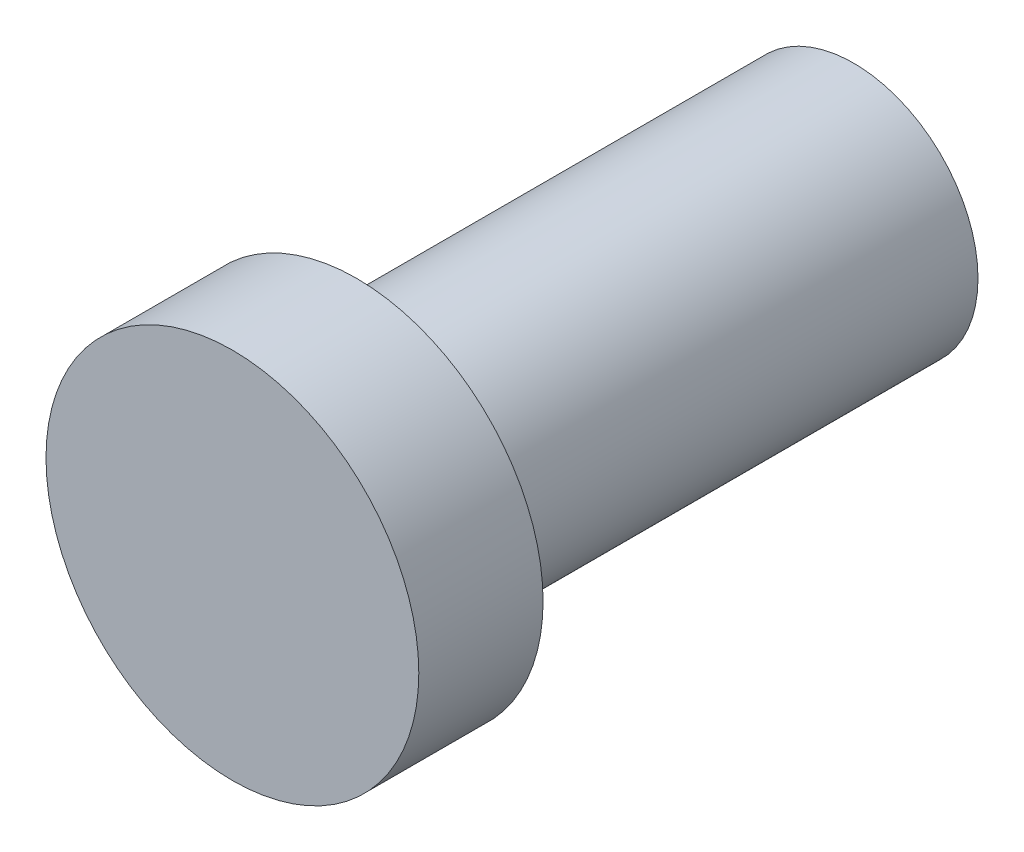
SolidWorks part; units mm, degrees
ref_plane "Alzado" through (0, 0, 0) normal (0, 0, 1) x (1, 0, 0)
ref_plane "Planta" through (0, 0, 0) normal (0, 1, 0) x (1, 0, 0)
ref_plane "Vista lateral" through (0, 0, 0) normal (1, 0, 0) x (0, 0, -1)
sketch "Croquis1" plane through (0, 0, 0) normal (0, 0, 1) x (1, 0, 0)
  circle A0 centre (0, 0) radius 6.35
  dimension "D1" = 12.7
extrude "Saliente-Extruir1" add sketch "Croquis1" along normal blind 25.4
sketch "Croquis2" plane through (0, 0, 25.4) normal (0, 0, 1) x (1, 0, 0)
  circle A0 centre (0, 0) radius 9.525
  dimension "D1" = 19.05
extrude "Saliente-Extruir2" add sketch "Croquis2" along normal blind 6.35
